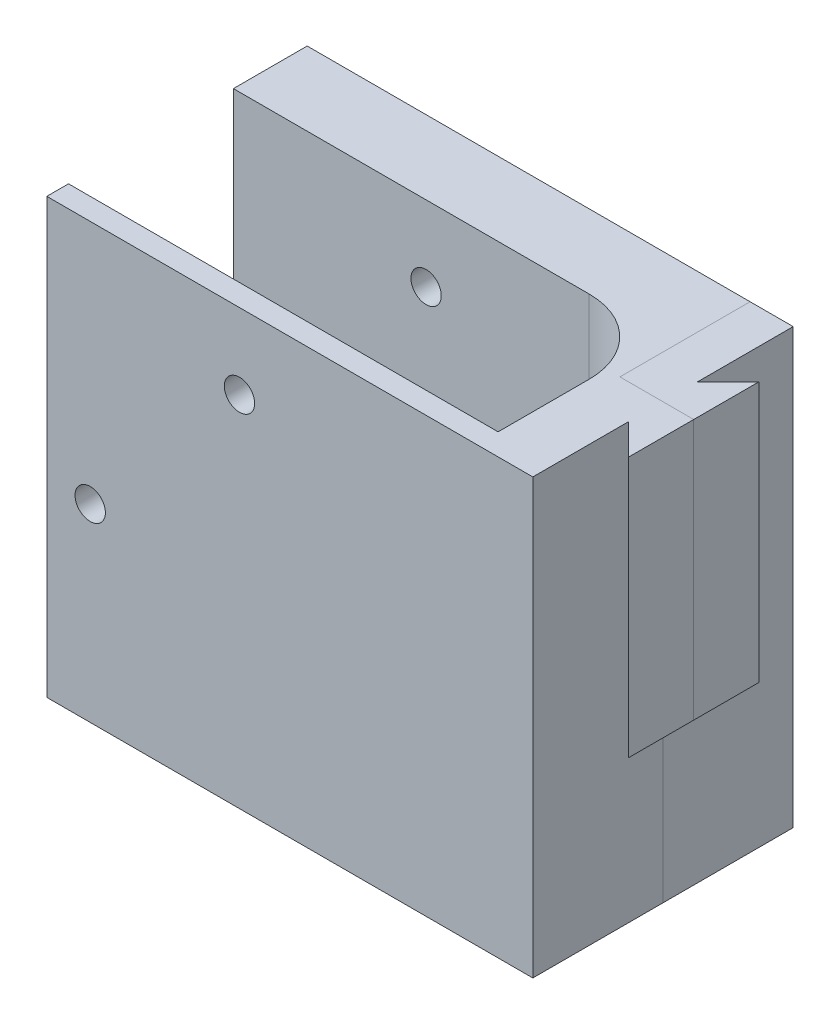
SolidWorks part; units mm, degrees
ref_plane "Front Plane" through (0, 0, 0) normal (0, 0, 1) x (1, 0, 0)
ref_plane "Top Plane" through (0, 0, 0) normal (0, 1, 0) x (1, 0, 0)
ref_plane "Right Plane" through (0, 0, 0) normal (1, 0, 0) x (0, 0, -1)
sketch "Sketch1" plane through (0, 0, 0) normal (0, 0, 1) x (1, 0, 0)
  line L1 (0, 0) -> (56, 0)
  line L2 (0, 0) -> (0, 50)
  line L3 (0, 50) -> (56, 50)
  line L4 (56, 0) -> (56, 50)
  dimension "D1" = 56
  dimension "D2" = 50
extrude "Boss-Extrude1" add sketch "Sketch1" along normal blind 30 contours L2 L3 L4 L1
sketch "Sketch2" plane through (0, 0, 0) normal (0, 0, -1) x (-1, 0, 0)
  line L0 (0, 0) -> (0, 50) construction
  line L1 (0, 0) -> (-56, 0) construction
  circle A0 centre (-22.2, 41.3) radius 1.75
  circle A1 centre (-5, 21.8) radius 1.75
  circle A2 centre (-48.4, 30.5) radius 3.55
  circle A3 centre (-34, 30.5) radius 3.55
  circle A4 centre (-44.5, 43) radius 5.5
  circle A5 centre (-24, 3.5) radius 5.5
  dimension "D1" = 7.1
  dimension "D2" = 7.1
  dimension "D4" = 11
  dimension "D5" = 11
  dimension "D6" = 3.5
  dimension "D7" = 3.5
  dimension "D3" = 0
  dimension "D8" = 14.4
  dimension "D9" = 10.8
  dimension "D10" = 11.8
  dimension "D11" = 12.5
  dimension "D12" = 10.5
  dimension "D13" = 10
  dimension "D14" = 27
  dimension "D15" = 29
  dimension "D16" = 8.7
  dimension "D17" = 5
  dimension "D18" = 3.5
sketch "Sketch4" plane through (0, 0, 0) normal (0, 0, -1) x (-1, 0, 0)
  circle A0 centre (-5, 21.8) radius 1.75 construction
  circle A1 centre (-22.2, 41.3) radius 1.75 construction
  circle A2 centre (-5, 21.8) radius 1.75
  circle A3 centre (-22.2, 41.3) radius 1.75
extrude "Cut-Extrude2" cut sketch "Sketch4" against normal through all
sketch "Sketch5" plane through (0, 50, 0) normal (0, 1, 0) x (1, 0, 0)
  line L0 (56, -30) -> (56, 0) construction
  line L1 (0, 0) -> (56, 0) construction
  line L2 (49.5, -17) -> (49.5, -27.5)
  line L4 (0, -30) -> (0, 0) construction
  line L5 (0, -27.5) -> (0, -8.5)
  line L6 (0, -8.5) -> (41, -8.5)
  line L11 (49.5, -27.5) -> (0, -27.5)
  arc A0 (49.5, -17) -> (41, -8.5) centre (41, -17) ccw
  dimension "D1" = 17
  dimension "D2" = 15
  dimension "D3" = 17
  dimension "D4" = 19
extrude "Cut-Extrude3" cut sketch "Sketch5" against normal through all
sketch "Sketch6" plane through (0, 0, 0) normal (0, 0, -1) x (-1, 0, 0)
  line L1 (0, 50) -> (-9, 50)
  line L2 (0, 50) -> (0, 26.8)
  line L3 (0, 26.8) -> (-9, 26.8)
  line L4 (-9, 50) -> (-9, 26.8)
  line L5 (0, 0) -> (-9, 0)
  line L6 (0, 0) -> (0, 16.8)
  line L7 (0, 16.8) -> (-9, 16.8)
  line L8 (-9, 0) -> (-9, 16.8)
  dimension "D1" = 9
  dimension "D2" = 9
  dimension "D3" = 10
  dimension "D4" = 5
sketch "Sketch7" plane through (0, 50, 0) normal (0, 1, 0) x (1, 0, 0)
  line L0 (59.5355, -7.5) -> (59.5355, -22.5)
  line L1 (59.5355, -22.5) -> (56, -18.9645)
  line L2 (59.5355, -7.5) -> (56, -11.0355)
  line L4 (56, -30) -> (56, 0) construction
  line L6 (56, -11.0355) -> (55, -11.0355)
  line L7 (55, -11.0355) -> (55, -18.9645)
  line L8 (55, -18.9645) -> (56, -18.9645)
  dimension "D1" = 15
  dimension "D2" = 5
  dimension "D3" = 315
  dimension "D4" = 135
  dimension "D5" = 5
  dimension "D6" = 7.5
  dimension "D7" = 0
  dimension "D8" = 1
ref_plane "Plane1" through (0, 20, 0) normal (0, 1, 0) x (1, 0, 0)
sketch "Sketch8" plane through (0, 20, 0) normal (0, 1, 0) x (1, 0, 0)
  line L3 (62.1602, -22.5) -> (58.6247, -18.9645)
  line L4 (62.1602, -7.5) -> (58.6247, -11.0355)
  line L5 (62.1602, -7.5) -> (62.1602, -22.5)
  line L8 (58.6247, -11.0355) -> (56, -11.0355)
  line L9 (56, -11.0355) -> (56, -18.9645) construction
  line L10 (56, -18.9645) -> (58.6247, -18.9645)
  line L11 (56, -30) -> (56, 0) construction
  line L12 (56, -11.0355) -> (55.5, -11.0355)
  line L13 (55.5, -11.0355) -> (55.5, -18.9645)
  line L14 (55.5, -18.9645) -> (56, -18.9645)
  dimension "D1" = 315
  dimension "D2" = 135
  dimension "D3" = 15
  dimension "D4" = 5
  dimension "D5" = 5
  dimension "D6" = 6.1602
  dimension "D7" = 1
extrude "Boss-Extrude2" add sketch "Sketch7" against normal blind 30
sketch "Sketch3" plane through (0, 0, 0) normal (0, 0, -1) x (-1, 0, 0)
  circle A0 centre (-24, 3.5) radius 5.5 construction
  circle A1 centre (-44.5, 43) radius 5.5 construction
  circle A2 centre (-24, 3.5) radius 5.5
  circle A3 centre (-44.5, 43) radius 5.5
  circle A4 centre (-34, 30.5) radius 3.55 construction
  circle A5 centre (-48.4, 30.5) radius 3.55 construction
  circle A6 centre (-34, 30.5) radius 3.55
  circle A7 centre (-48.4, 30.5) radius 3.55
extrude "Cut-Extrude1" [suppressed] cut sketch "Sketch3" against normal blind 6
sketch "Sketch9" plane through (0, 50, 0) normal (0, 1, 0) x (1, 0, 0)
  line L0 (59.5355, -22.5) -> (59.5355, -7.5) construction
  line L1 (71.0355, -15) -> (51.0355, -15)
  line L2 (71.0355, -15) -> (71.0355, 5)
  line L3 (71.0355, 5) -> (51.0355, 5)
  line L4 (51.0355, -15) -> (51.0355, 5)
  dimension "D1" = 7.5
  dimension "D2" = 8.5
  dimension "D3" = 20
  dimension "D4" = 20
split "Split1" trim tools "Sketch9" bodies to split 126 resulting bodies 127 128
equation "\"D2@Sketch2\"=\"D1@Sketch2\""
